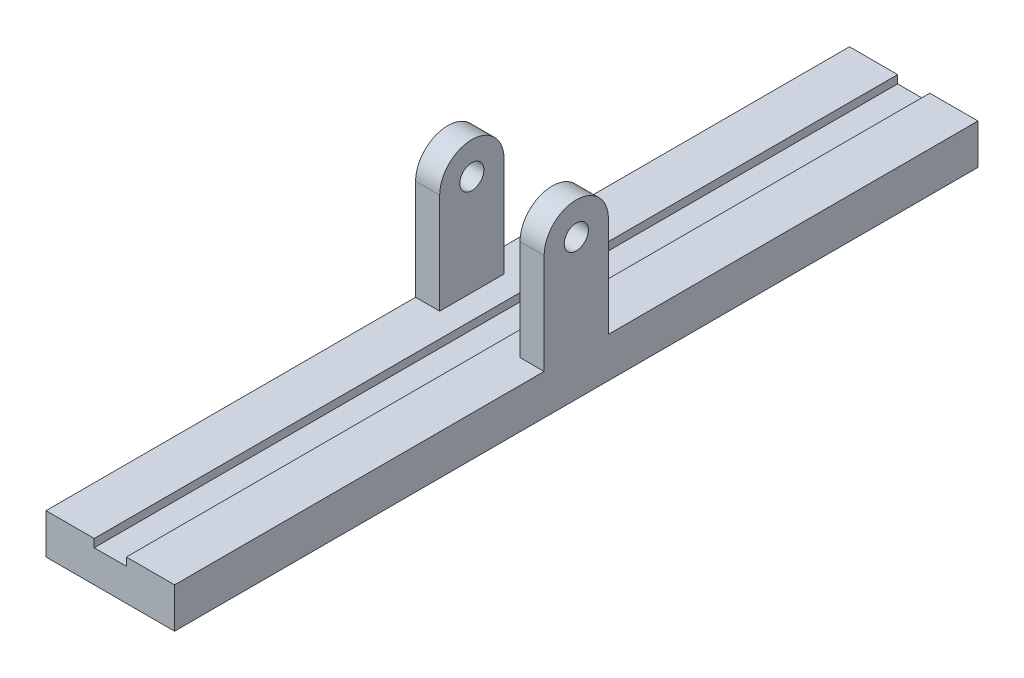
SolidWorks part; units mm, degrees
ref_plane "Ön Düzlem" through (0, 0, 0) normal (0, 0, 1) x (1, 0, 0)
ref_plane "Üst Düzlem" through (0, 0, 0) normal (0, 1, 0) x (1, 0, 0)
ref_plane "Sağ Düzlem" through (0, 0, 0) normal (1, 0, 0) x (0, 0, -1)
sketch "Çizim2" plane through (0, 0, 0) normal (0, 0, 1) x (1, 0, 0)
  line L0 (10, 25) -> (40, 25)
  line L1 (-40, 25) -> (-10, 25)
  line L2 (-40, 25) -> (-40, 0)
  line L3 (-40, 0) -> (40, 0)
  line L4 (40, 25) -> (40, 0)
  line L5 (-10, 25) -> (-10, 20)
  line L6 (-10, 20) -> (10, 20)
  line L7 (10, 25) -> (10, 20)
  point P4 (0, 0)
  dimension "D1" = 20
  dimension "D2" = 5
  dimension "D3" = 25
  dimension "D4" = 30
  dimension "D5" = 80
extrude "Yükseklik-Ekstrüzyon1" add sketch "Çizim2" along normal mid plane 500
sketch "Çizim3" plane through (40, 0, 0) normal (1, 0, 0) x (0, 0, -1)
  line L0 (-250, 25) -> (250, 25) construction
  line L1 (-20, 25) -> (20, 25)
  line L2 (-20, 25) -> (-20, 87.5)
  line L3 (-20, 87.5) -> (20, 87.5) construction
  line L4 (20, 25) -> (20, 87.5)
  arc A0 (20, 87.5) -> (-20, 87.5) centre (0, 87.5) ccw
  circle A1 centre (0, 87.5) radius 7.5
  dimension "D1" = 20
  dimension "D4" = 15
  dimension "D2" = 20
  dimension "D3" = 62.5
extrude "Yükseklik-Ekstrüzyon3" add sketch "Çizim3" against normal blind 15
ref_plane "Düzlem1" through (0, 0, 0) normal (-1, 0, 0) x (0, 0, 1)
mirror "Aynalama1" about plane through (0, 0, 0) normal (-1, 0, 0) of "Yükseklik-Ekstrüzyon3"
